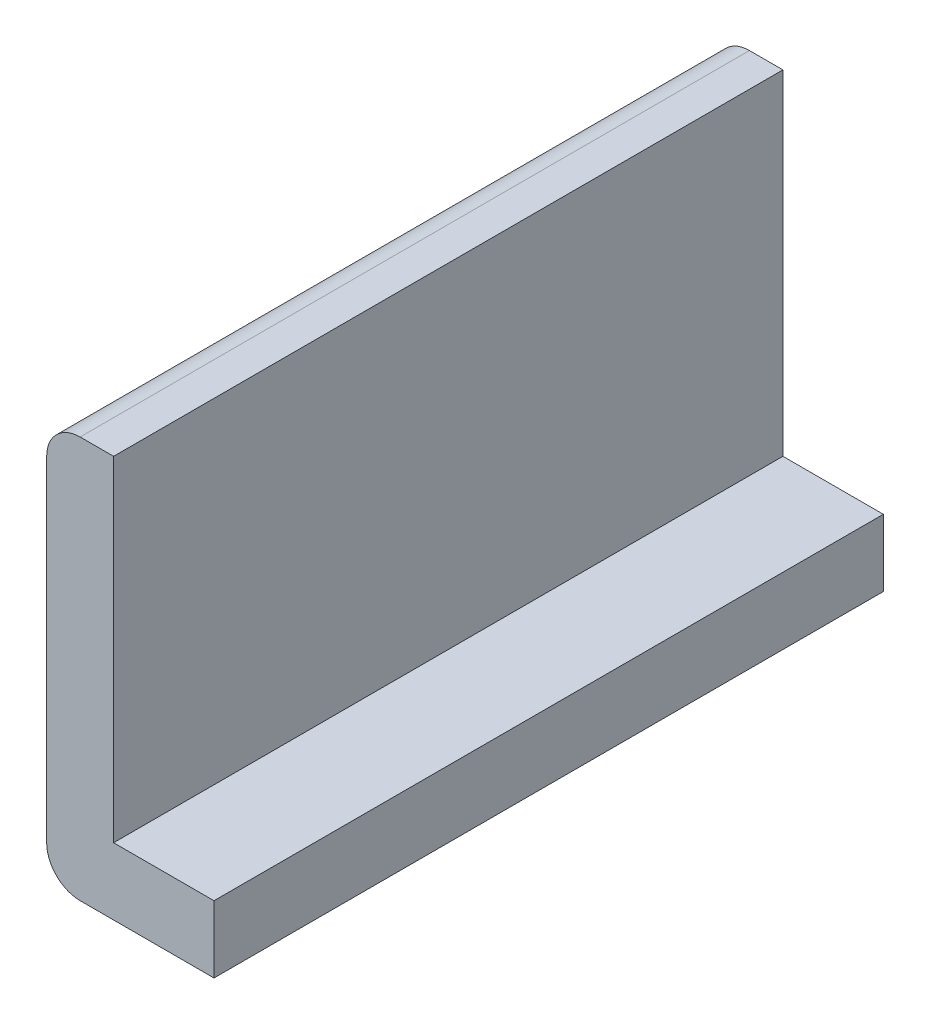
SolidWorks part; units mm, degrees
ref_plane "Plan de face" through (0, 0, 0) normal (0, 0, 1) x (1, 0, 0)
ref_plane "Plan de dessus" through (0, 0, 0) normal (0, 1, 0) x (1, 0, 0)
ref_plane "Plan de droite" through (0, 0, 0) normal (1, 0, 0) x (0, 0, -1)
sketch "Esquisse1" plane through (0, 0, 0) normal (0, 0, 1) x (1, 0, 0)
  line L0 (0, 0.1) -> (0, 1.1)
  line L1 (0.1, 0) -> (0.5, 0)
  line L2 (0.1, 1.2) -> (0.2, 1.2)
  line L3 (0.2, 0.2) -> (0.5, 0.2)
  line L4 (0.2, 0.2) -> (0.2, 1.2)
  line L5 (0.5, 0.2) -> (0.5, 0)
  line L6 (0.2, 0.2) -> (0.2, 1) construction
  line L7 (0.1, 1.2) -> (0.4365, 1.2) construction
  line L8 (0.2, 1) -> (0.4365, 1) construction
  line L11 (0.2, 0.2) -> (0.5, 0.2) construction
  arc A0 (0, 1.1) -> (0.1, 1.2) centre (0.1, 1.1) cw
  arc A1 (0.1, 0) -> (0, 0.1) centre (0.1, 0.1) cw
  arc A4 (0.2, 1) -> (0.2, 1) centre (0.2, 1) cw construction
  arc A5 (0.2, 0.2) -> (0.2, 0.2) centre (0.2, 0.2) cw construction
  point P9 (0, 0)
  dimension "D1" = 0.1
  dimension "D2" = 0.2
extrude "Extrusion1" add sketch "Esquisse1" along normal blind 2
